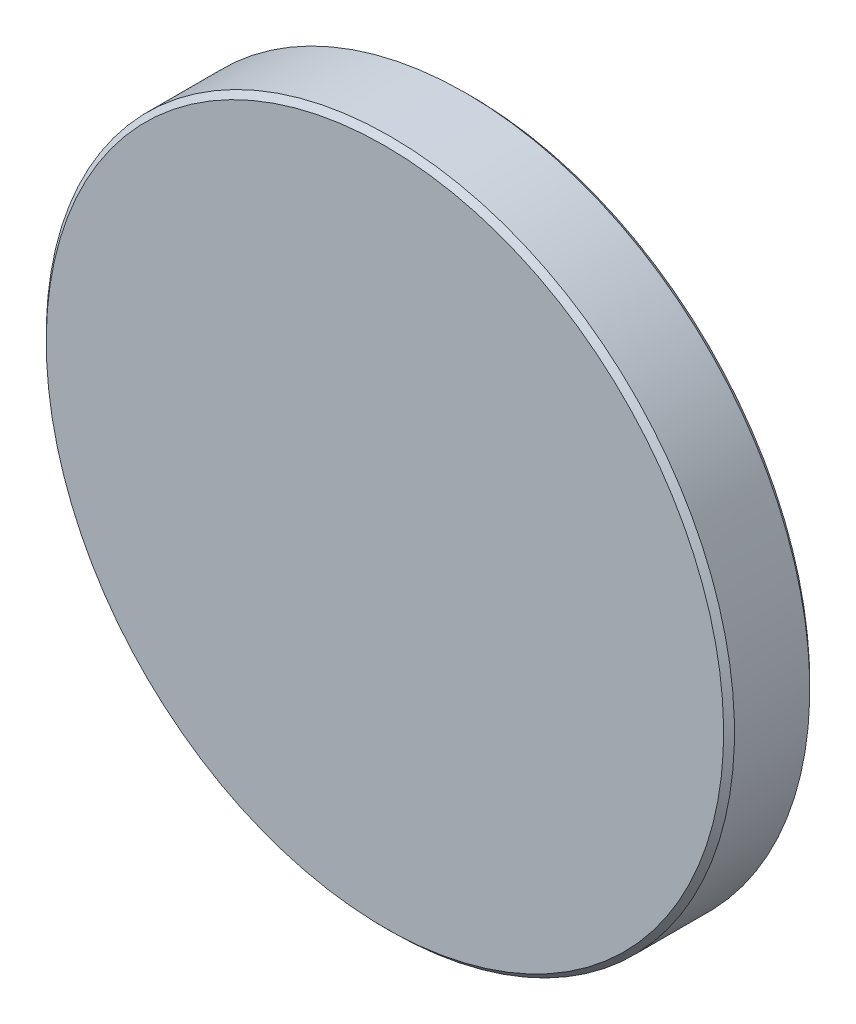
SolidWorks part; units mm, degrees
material "Al 6061-T6"
ref_plane "Front" through (0, 0, 0) normal (0, 0, 1) x (1, 0, 0)
ref_plane "Top" through (0, 0, 0) normal (0, 1, 0) x (1, 0, 0)
ref_plane "Right" through (0, 0, 0) normal (1, 0, 0) x (0, 0, -1)
sketch "Sketch1" plane through (0, 0, 0) normal (1, 0, 0) x (0, 0, -1)
  line L0 (-662.018, 0) -> (662.018, 0) construction
  line L1 (-458.4143, 54) -> (-458.4143, 63.3349)
  line L2 (-458.4143, 63.3349) -> (-442.5558, 63.3349)
  line L3 (-442.5558, 63.3349) -> (-442.5558, 54)
  line L4 (-451.375, 0) -> (-443.875, 0)
  arc A0 (-458.4143, 54) -> (-451.375, 0) centre (-662.018, 0) cw
  arc A1 (-443.875, 0) -> (-442.5558, 54) centre (662.018, 0) cw
  point P3 (0, 0)
revolve "Revolve3" add sketch "Sketch1" angle 360 about L0
chamfer "Chamfer1" distance 1 angle 45 2 edges at (0, -63.3349, 442.5558) (0, -63.3349, 458.4143)
ref_plane "Plane1" through (0, 0, 443.875) normal (0, 0, -1) x (-1, 0, 0)
sketch "Sketch2" plane through (0, 0, 458.4143) normal (0, 0, 1) x (1, 0, 0)
  circle A1 centre (0, 0) radius 62.3349
  circle A2 centre (0, 0) radius 62.3349
  circle M3 centre (0, 0) radius 54
  dimension "D1" = 0
extrude "Boss-Extrude1" add sketch "Sketch2" against normal up to surface (15.8585 mm away) contours M3 up to face at (0, -62.3349, 442.5558)
equation "\"D3@Sketch1\"=210.643+7.5+1105.893"
equation "\"D6@Sketch1\"=4.987*25.4/2"
